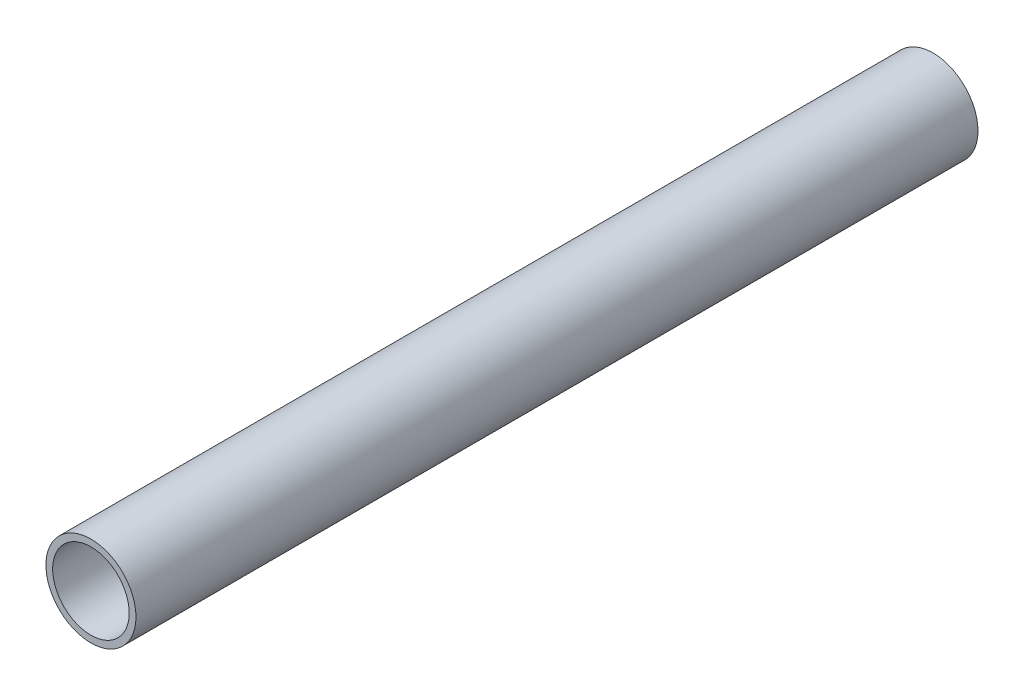
SolidWorks part; units mm, degrees
ref_plane "Front Plane" through (0, 0, 0) normal (0, 0, 1) x (1, 0, 0)
ref_plane "Top Plane" through (0, 0, 0) normal (0, 1, 0) x (1, 0, 0)
ref_plane "Right Plane" through (0, 0, 0) normal (1, 0, 0) x (0, 0, -1)
sketch "Sketch1" plane through (0, 0, 0) normal (0, 0, 1) x (1, 0, 0)
  circle A0 centre (0, 0) radius 12.7
  circle A1 centre (0, 0) radius 10.795
  dimension "D1" = 25.4
  dimension "D2" = 21.59
extrude "Boss-Extrude1" add sketch "Sketch1" along normal blind 237.49
